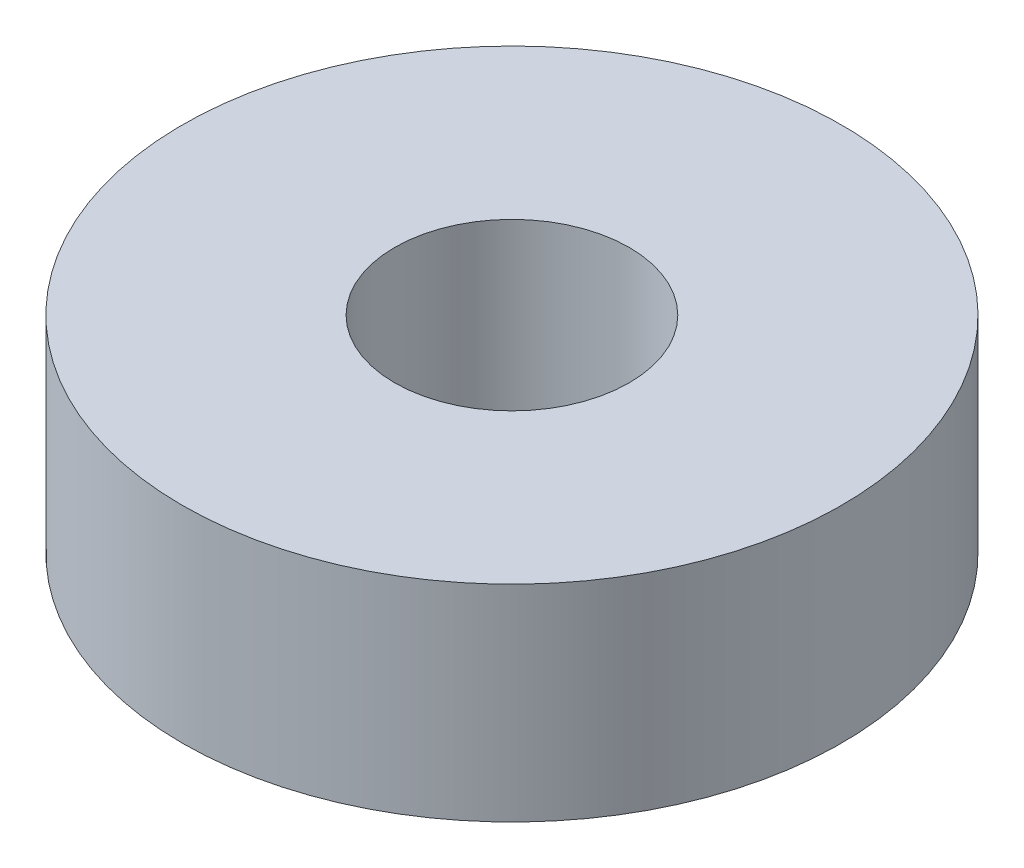
SolidWorks part; units mm, degrees
ref_plane "Front Plane" through (0, 0, 0) normal (0, 0, 1) x (1, 0, 0)
ref_plane "Top Plane" through (0, 0, 0) normal (0, 1, 0) x (1, 0, 0)
ref_plane "Right Plane" through (0, 0, 0) normal (1, 0, 0) x (0, 0, -1)
sketch "草圖1" plane through (0, 0, 0) normal (0, 1, 0) x (1, 0, 0)
  circle A0 centre (0, 0) radius 16
  dimension "D1" = 32
extrude "填料-伸長1" add sketch "草圖1" along normal blind 10
sketch "草圖2" plane through (0, 10, 0) normal (0, 1, 0) x (1, 0, 0)
  circle A0 centre (0, 0) radius 5.6946
extrude "除料-伸長1" cut sketch "草圖2" against normal through all
